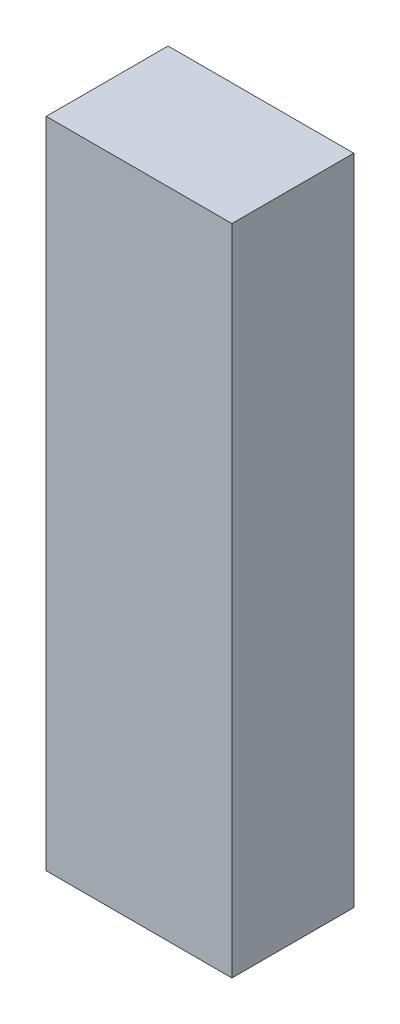
SolidWorks part; units mm, degrees
ref_plane "Front Plane" through (0, 0, 0) normal (1, 0, 0) x (0, 1, 0)
ref_plane "Top Plane" through (0, 0, 0) normal (0, 0, 1) x (0, 1, 0)
ref_plane "Right Plane" through (0, 0, 0) normal (0, 1, 0) x (-1, 0, 0)
sketch "Sketch2" plane through (0, 0, 0) normal (0, 0, 1) x (0, 1, 0)
  line L1 (84.455, -24.003) -> (-84.455, -24.003)
  line L2 (84.455, -24.003) -> (84.455, 24.003)
  line L3 (84.455, 24.003) -> (-84.455, 24.003)
  line L4 (-84.455, -24.003) -> (-84.455, 24.003)
  line L5 (84.455, -24.003) -> (-84.455, 24.003) construction
  line L6 (84.455, 24.003) -> (-84.455, -24.003) construction
  point P0 (0, 0)
  dimension "D1" = 168.91
  dimension "D2" = 48.006
extrude "Boss-Extrude1" add sketch "Sketch2" along normal blind 31.496
